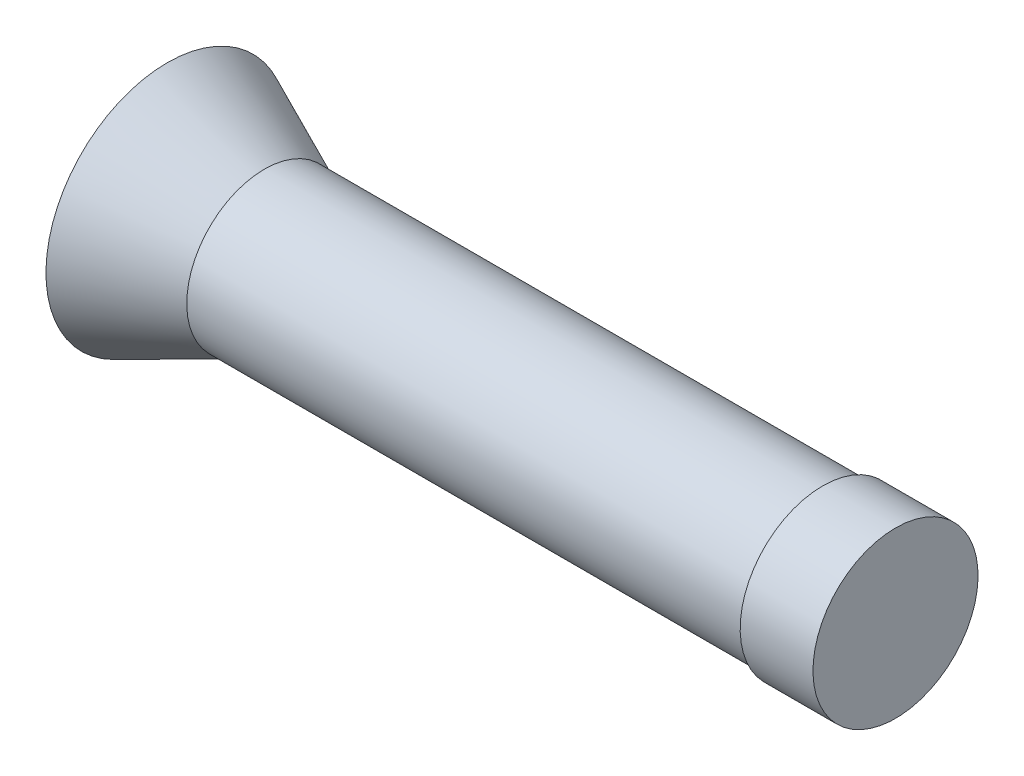
SolidWorks part; units mm, degrees
ref_plane "Front Plane" through (0, 0, 0) normal (0, 0, 1) x (1, 0, 0)
ref_plane "Top Plane" through (0, 0, 0) normal (0, 1, 0) x (1, 0, 0)
ref_plane "Right Plane" through (0, 0, 0) normal (1, 0, 0) x (0, 0, -1)
sketch "Sketch1" plane through (0, 0, 0) normal (0, 0, 1) x (1, 0, 0)
  line L0 (-115, 0) -> (-135, 9)
  line L1 (0, 0) -> (-115, 0)
  line L2 (0, 0) -> (0, 1)
  line L3 (0, 1) -> (15, 1)
  line L4 (15, 1) -> (15, -16)
  line L5 (15, -16) -> (-135, -16)
  line L6 (-135, -16) -> (-135, 9)
  dimension "D1" = 150
  dimension "D2" = 17
  dimension "D3" = 16
  dimension "D4" = 25
  dimension "D5" = 20
  dimension "D6" = 15
revolve "Revolve1" add sketch "Sketch1" angle 360 about L5
sketch "Sketch2" plane through (-135, 0, 0) normal (-1, 0, 0) x (0, 0, 1)
  circle A0 centre (0, -16) radius 15
  dimension "D1" = 30
extrude "Cut-Extrude1" cut sketch "Sketch2" against normal blind 145 contours A0
